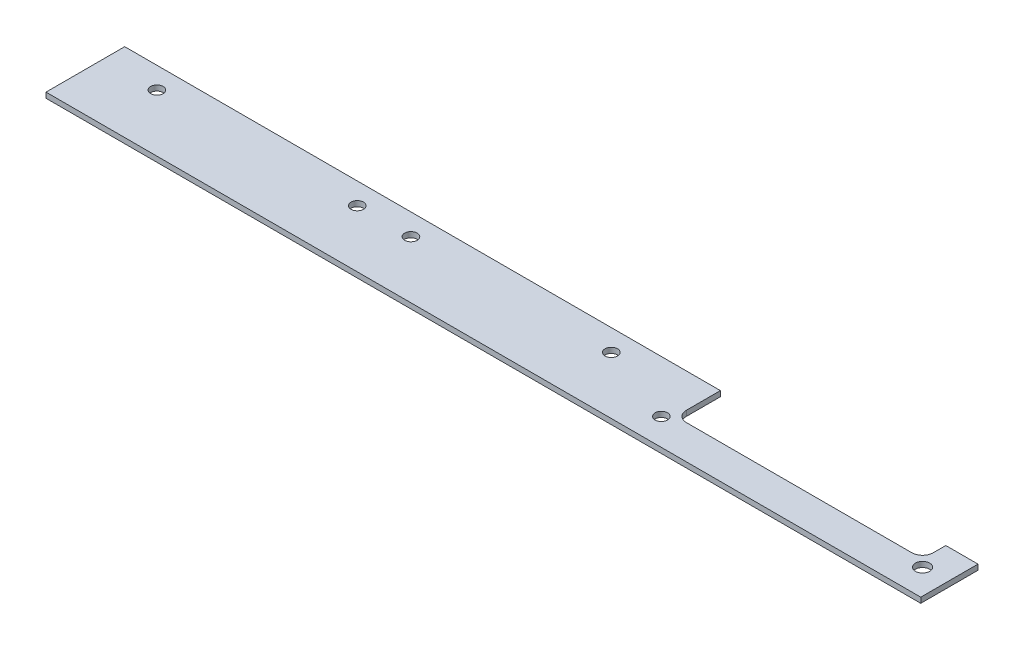
SolidWorks part; units mm, degrees
material "Простая углеродистая сталь"
ref_plane "Спереди" through (0, 0, 0) normal (0, 0, 1) x (1, 0, 0)
ref_plane "Сверху" through (0, 0, 0) normal (0, 1, 0) x (1, 0, 0)
ref_plane "Справа" through (0, 0, 0) normal (1, 0, 0) x (0, 0, -1)
sketch "Эскиз1" plane through (0, 0, 0) normal (0, 1, 0) x (1, 0, 0)
  line L0 (166.5, 22) -> (166.5, 12.5)
  line L1 (0, 0) -> (244.5, 0)
  line L2 (0, 0) -> (0, 22)
  line L3 (0, 22) -> (166.5, 22)
  line L5 (169.5, 9.5) -> (232.5, 9.5)
  line L7 (235.5, 12.5) -> (235.5, 16)
  line L8 (235.5, 16) -> (244.5, 16)
  line L9 (244.5, 16) -> (244.5, 0)
  circle A1 centre (164.5, 7.5) radius 1.75
  circle A2 centre (71, 16) radius 1.75
  circle A3 centre (15, 16) radius 1.75
  circle A4 centre (86, 16) radius 1.75
  circle A5 centre (142, 16) radius 1.75
  circle A8 centre (237.5, 7.5) radius 2
  arc A9 (166.5, 12.5) -> (169.5, 9.5) centre (169.5, 12.5) ccw
  arc A10 (232.5, 9.5) -> (235.5, 12.5) centre (232.5, 12.5) ccw
  dimension "D2" = 3
  dimension "D3" = 3
  dimension "D1" = 2
extrude "Бобышка-Вытянуть1" add sketch "Эскиз1" along normal blind 1.5 contours L2 L1 L3
